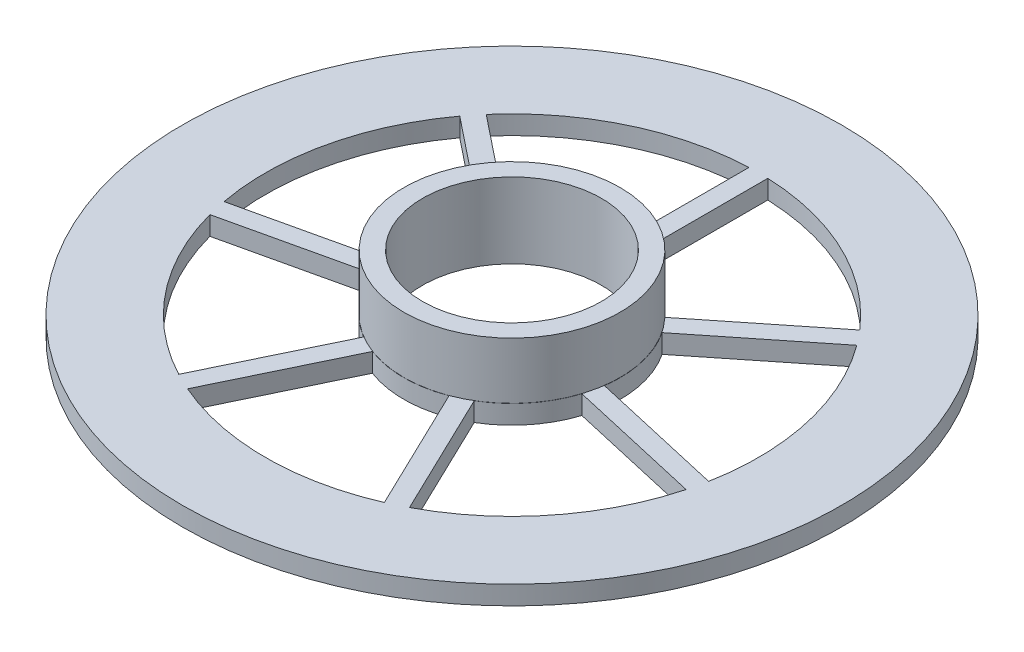
SolidWorks part; units mm, degrees
ref_plane "前视基准面" through (0, 0, 0) normal (0, 0, 1) x (1, 0, 0)
ref_plane "上视基准面" through (0, 0, 0) normal (0, 1, 0) x (1, 0, 0)
ref_plane "右视基准面" through (0, 0, 0) normal (1, 0, 0) x (0, 0, -1)
sketch "草图1" plane through (0, 0, 0) normal (0, 1, 0) x (1, 0, 0)
  line L0 (0, -998.2286) -> (0, 9.5) construction
  line L1 (19.8329, 17.0952) -> (8.3335, 7.9248)
  line L2 (0, 10.4676) -> (0, 50001.7714) construction
  line L3 (-1, 26.1647) -> (-1, 11.4564)
  line L5 (1, 26.1647) -> (1, 11.4564)
  line L7 (21.0798, 15.5316) -> (9.5805, 6.3611)
  line L9 (25.7312, -4.8473) -> (11.3917, -1.5744)
  line L11 (25.2861, -6.7971) -> (10.9467, -3.5242)
  line L13 (12.2534, -23.1397) -> (5.8717, -9.888)
  line L15 (10.4515, -24.0074) -> (4.0698, -10.7558)
  line L17 (-10.4515, -24.0074) -> (-4.0698, -10.7558)
  line L19 (-12.2534, -23.1397) -> (-5.8717, -9.888)
  line L21 (-25.2861, -6.7971) -> (-10.9467, -3.5242)
  line L23 (-25.7312, -4.8473) -> (-11.3917, -1.5744)
  line L25 (-21.0798, 15.5316) -> (-9.5805, 6.3611)
  line L27 (-19.8329, 17.0952) -> (-8.3335, 7.9248)
  circle A0 centre (0, 0) radius 9.5
  arc A1 (-1, 11.4564) -> (-8.3335, 7.9248) centre (0, 0) ccw
  arc A2 (-21.0798, 15.5316) -> (-25.7312, -4.8473) centre (0, 0) ccw
  circle A3 centre (0, 0) radius 35
  arc A4 (-1, 26.1647) -> (-19.8329, 17.0952) centre (0, 0) ccw
  arc A5 (19.8329, 17.0952) -> (1, 26.1647) centre (0, 0) ccw
  arc A6 (25.7312, -4.8473) -> (21.0798, 15.5316) centre (0, 0) ccw
  arc A7 (12.2534, -23.1397) -> (25.2861, -6.7971) centre (0, 0) ccw
  arc A8 (-10.4515, -24.0074) -> (10.4515, -24.0074) centre (0, 0) ccw
  arc A9 (-25.2861, -6.7971) -> (-12.2534, -23.1397) centre (0, 0) ccw
  arc A10 (8.3335, 7.9248) -> (1, 11.4564) centre (0, 0) ccw
  arc A11 (11.3917, -1.5744) -> (9.5805, 6.3611) centre (0, 0) ccw
  arc A12 (5.8717, -9.888) -> (10.9467, -3.5242) centre (0, 0) ccw
  arc A13 (-4.0698, -10.7558) -> (4.0698, -10.7558) centre (0, 0) ccw
  arc A14 (-10.9467, -3.5242) -> (-5.8717, -9.888) centre (0, 0) ccw
  arc A15 (-9.5805, 6.3611) -> (-11.3917, -1.5744) centre (0, 0) ccw
  point P38 (0, 0)
  dimension "D1" = 19
  dimension "D2" = 23
  dimension "D3" = 70
  dimension "D4" = 7
extrude "凸台-拉伸1" add sketch "草图1" along normal blind 18
sketch "草图2" plane through (0, 18, 0) normal (0, 1, 0) x (1, 0, 0)
  circle A0 centre (0, 0) radius 40.8564
  circle A1 centre (0, 0) radius 11.4826
extrude "切除-拉伸1" cut sketch "草图2" against normal blind 16
sketch "草图3" plane through (0, 18, 0) normal (0, 1, 0) x (1, 0, 0)
  circle A0 centre (0, 0) radius 16.8114
extrude "切除-拉伸2" cut sketch "草图3" against normal blind 10
